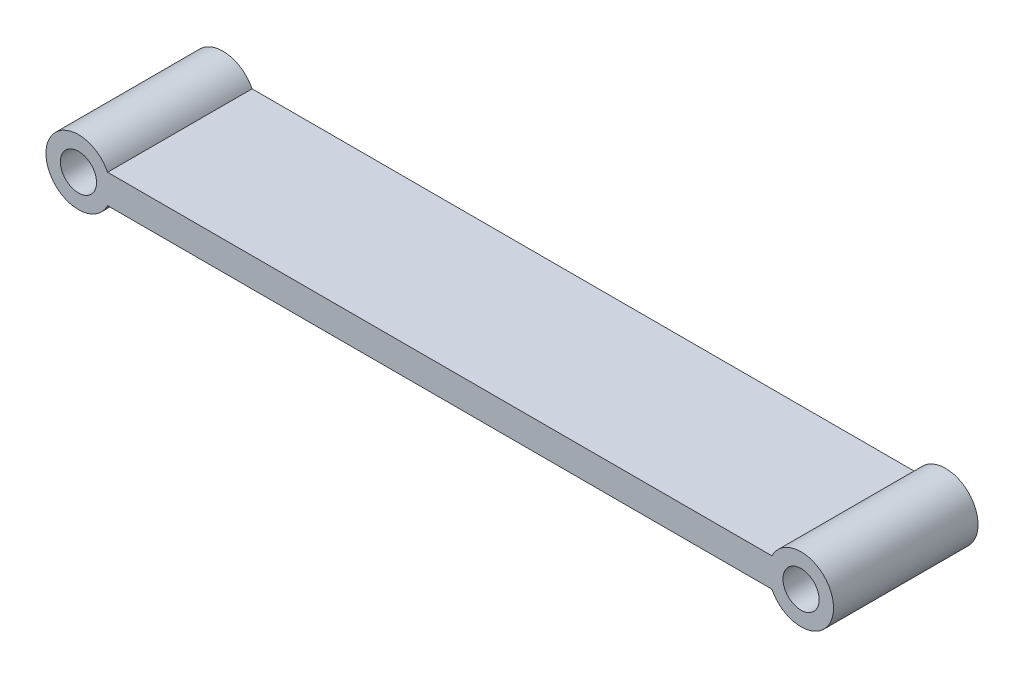
SolidWorks part; units mm, degrees
ref_plane "Front Plane" through (0, 0, 0) normal (0, 0, 1) x (1, 0, 0)
ref_plane "Top Plane" through (0, 0, 0) normal (0, 1, 0) x (1, 0, 0)
ref_plane "Right Plane" through (0, 0, 0) normal (1, 0, 0) x (0, 0, -1)
sketch "Sketch1" plane through (0, 0, 0) normal (0, 0, 1) x (1, 0, 0)
  line L0 (0, 0) -> (127, 0) construction
  line L1 (5.1195, 2.54) -> (121.8805, 2.54)
  line L2 (5.1195, -2.54) -> (121.8805, -2.54)
  circle A0 centre (0, 0) radius 3.175
  circle A1 centre (127, 0) radius 3.175
  arc A2 (5.1195, 2.54) -> (5.1195, -2.54) centre (0, 0) ccw
  arc A3 (121.8805, -2.54) -> (121.8805, 2.54) centre (127, 0) ccw
  circle A4 centre (0, 0) radius 5.715 construction
  circle A5 centre (127, 0) radius 5.715 construction
  dimension "D1" = 127
  dimension "D2" = 6.35
  dimension "D4" = 2.54
  dimension "D3" = 2.54
extrude "Boss-Extrude1" add sketch "Sketch1" along normal mid plane 25.4
